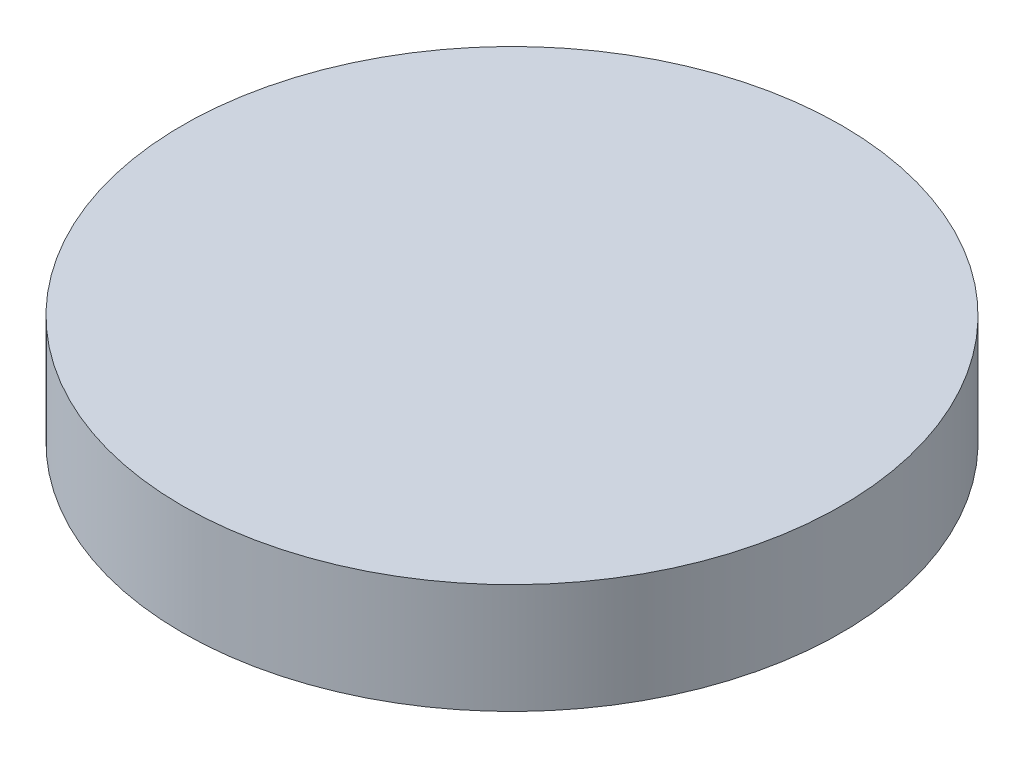
SolidWorks part; units mm, degrees
ref_plane "Front Plane" through (0, 0, 0) normal (0, 0, 1) x (1, 0, 0)
ref_plane "Top Plane" through (0, 0, 0) normal (0, 1, 0) x (1, 0, 0)
ref_plane "Right Plane" through (0, 0, 0) normal (1, 0, 0) x (0, 0, -1)
sketch "Sketch1" plane through (0, 0, 0) normal (0, 1, 0) x (1, 0, 0)
  circle A0 centre (-47.7088, -19.327) radius 19.05
  dimension "D1" = 38.1
extrude "Boss-Extrude1" add sketch "Sketch1" along normal blind 6.35
sketch "Sketch2" plane through (0, 6.35, 0) normal (0, 1, 0) x (1, 0, 0)
  circle A2 centre (-47.7088, -19.327) radius 19.25
  circle A3 centre (-47.7088, -19.327) radius 19.25
  dimension "D1" = 0.2
